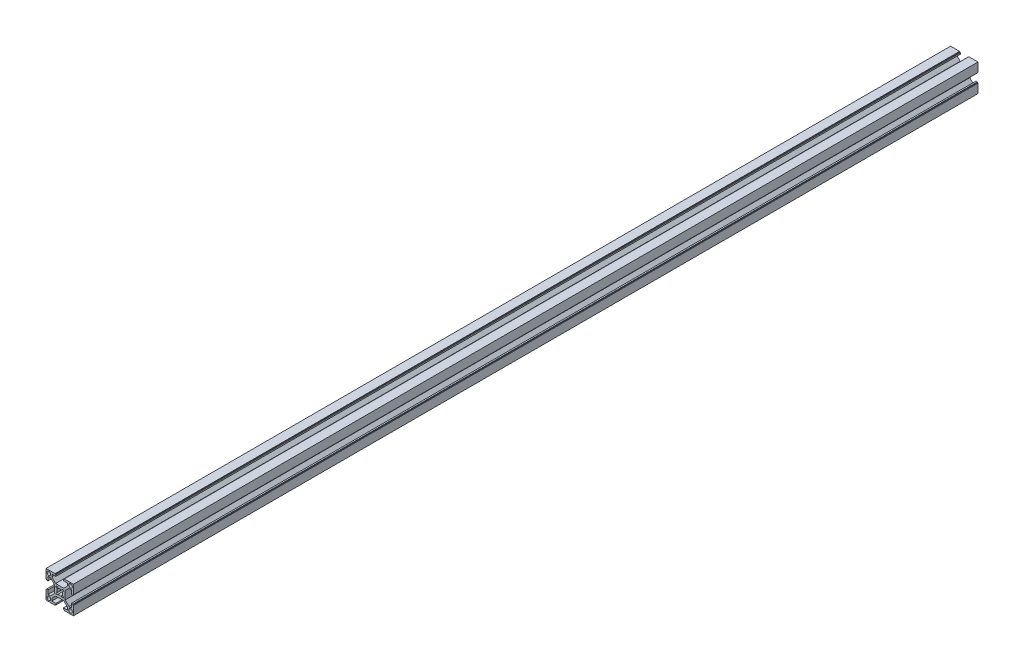
SolidWorks part; units mm, degrees
ref_plane "Front Plane" through (0, 0, 0) normal (0, 0, 1) x (1, 0, 0)
ref_plane "Top Plane" through (0, 0, 0) normal (0, 1, 0) x (1, 0, 0)
ref_plane "Right Plane" through (0, 0, 0) normal (1, 0, 0) x (0, 0, -1)
sketch "Sketch2" plane through (0, 0, 0) normal (0, 0, 1) x (1, 0, 0)
  line L0 (0, 0) -> (0, 10)
  line L1 (0, 0) -> (10, 0)
  line L2 (0, 10) -> (0.7, 10)
  line L3 (0.7, 10) -> (0.7, 10.9)
  line L4 (0.7, 10.9) -> (2.2, 10.9)
  line L5 (2.2, 10.9) -> (2.2, 6.4)
  line L6 (10, 0) -> (10, 0.7)
  line L7 (10, 0.7) -> (10.9, 0.7)
  line L8 (10.9, 0.7) -> (10.9, 2.2)
  line L9 (10.9, 2.2) -> (6.4, 2.2)
  line L10 (2.2, 6.4) -> (4.9, 6.4)
  line L11 (6.4, 2.2) -> (6.4, 4.9)
  line L12 (6.4, 4.9) -> (10.6426, 9.1426)
  line L13 (4.9, 6.4) -> (9.1426, 10.6426)
  line L14 (6.4, 4.9) -> (18.1964, 4.9) construction
  line L15 (4.9, 6.4) -> (7.45, 6.4) construction
  line L16 (10.6426, 9.1426) -> (19.6426, 9.1426)
  line L17 (9.1426, 10.6426) -> (9.1426, 19.6426)
  line L18 (25.3853, 6.4) -> (22.8353, 6.4) construction
  line L19 (23.8853, 4.9) -> (12.0888, 4.9) construction
  line L20 (15.1426, 5.8755) -> (15.1426, 30.9243) construction
  line L21 (21.1426, 10.6426) -> (21.1426, 19.6426)
  line L22 (25.3853, 6.4) -> (21.1426, 10.6426)
  line L23 (23.8853, 4.9) -> (19.6426, 9.1426)
  line L24 (23.8853, 2.2) -> (23.8853, 4.9)
  line L25 (28.0853, 6.4) -> (25.3853, 6.4)
  line L26 (19.3853, 2.2) -> (23.8853, 2.2)
  line L27 (19.3853, 0.7) -> (19.3853, 2.2)
  line L28 (20.2853, 0.7) -> (19.3853, 0.7)
  line L29 (20.2853, 0) -> (20.2853, 0.7)
  line L30 (28.0853, 10.9) -> (28.0853, 6.4)
  line L31 (29.5853, 10.9) -> (28.0853, 10.9)
  line L32 (29.5853, 10) -> (29.5853, 10.9)
  line L33 (30.2853, 10) -> (29.5853, 10)
  line L34 (30.2853, 0) -> (20.2853, 0)
  line L35 (30.2853, 0) -> (30.2853, 10)
  line L36 (-3.9056, 15.1426) -> (38.0923, 15.1426) construction
  line L37 (15.1426, 24.4098) -> (15.1426, -0.6391) construction
  line L38 (23.8853, 25.3853) -> (12.0888, 25.3853) construction
  line L39 (25.3853, 23.8853) -> (22.8353, 23.8853) construction
  line L40 (4.9, 23.8853) -> (7.45, 23.8853) construction
  line L41 (6.4, 25.3853) -> (18.1964, 25.3853) construction
  line L42 (30.2853, 30.2853) -> (30.2853, 20.2853)
  line L43 (30.2853, 30.2853) -> (20.2853, 30.2853)
  line L44 (30.2853, 20.2853) -> (29.5853, 20.2853)
  line L45 (29.5853, 20.2853) -> (29.5853, 19.3853)
  line L46 (29.5853, 19.3853) -> (28.0853, 19.3853)
  line L47 (28.0853, 19.3853) -> (28.0853, 23.8853)
  line L48 (20.2853, 30.2853) -> (20.2853, 29.5853)
  line L49 (20.2853, 29.5853) -> (19.3853, 29.5853)
  line L50 (19.3853, 29.5853) -> (19.3853, 28.0853)
  line L51 (19.3853, 28.0853) -> (23.8853, 28.0853)
  line L52 (28.0853, 23.8853) -> (25.3853, 23.8853)
  line L53 (23.8853, 28.0853) -> (23.8853, 25.3853)
  line L54 (23.8853, 25.3853) -> (19.6426, 21.1426)
  line L55 (25.3853, 23.8853) -> (21.1426, 19.6426)
  line L56 (10.6426, 21.1426) -> (19.6426, 21.1426)
  line L57 (4.9, 23.8853) -> (9.1426, 19.6426)
  line L58 (6.4, 25.3853) -> (10.6426, 21.1426)
  line L59 (6.4, 28.0853) -> (6.4, 25.3853)
  line L60 (2.2, 23.8853) -> (4.9, 23.8853)
  line L61 (10.9, 28.0853) -> (6.4, 28.0853)
  line L62 (10.9, 29.5853) -> (10.9, 28.0853)
  line L63 (10, 29.5853) -> (10.9, 29.5853)
  line L64 (10, 30.2853) -> (10, 29.5853)
  line L65 (2.2, 19.3853) -> (2.2, 23.8853)
  line L66 (0.7, 19.3853) -> (2.2, 19.3853)
  line L67 (0.7, 20.2853) -> (0.7, 19.3853)
  line L68 (0, 20.2853) -> (0.7, 20.2853)
  line L69 (0, 30.2853) -> (10, 30.2853)
  line L70 (0, 30.2853) -> (0, 20.2853)
  point P29 (15.1426, 9.1426)
  point P65 (21.1426, 15.1426)
  point P66 (9.1426, 15.1426)
  point P78 (15.1426, 21.1426)
  dimension "D1" = 10
  dimension "D2" = 10
  dimension "D3" = 0.7
  dimension "D4" = 0.9
  dimension "D5" = 1.5
  dimension "D6" = 4.5
  dimension "D7" = 0.7
  dimension "D8" = 1.5
  dimension "D9" = 0.9
  dimension "D10" = 2.7
  dimension "D11" = 4.5
  dimension "D12" = 6
  dimension "D13" = 45
  dimension "D14" = 45
  dimension "D15" = 2.7
  dimension "D16" = 6
  dimension "D17" = 6
  dimension "D18" = 4.5
  dimension "D19" = 4.5
  dimension "D20" = 2.1213
extrude "Boss-Extrude2" add sketch "Sketch2" against normal blind 1000
sketch "Sketch3" plane through (0, 0, 0) normal (0, 0, 1) x (1, 0, 0)
  line L10 (15.1426, 15.1428) -> (15.1426, 11.8926) construction
  line L20 (3.2001, 27.0853) -> (18.9964, 11.2889) construction
  line L21 (11.2889, 17.865) -> (12.3496, 16.8044)
  line L22 (12.4203, 18.9964) -> (13.481, 17.9357)
  line L24 (17.865, 18.9964) -> (16.8043, 17.9357)
  line L25 (18.9964, 17.865) -> (17.9357, 16.8044)
  line L26 (18.9964, 12.4203) -> (17.9357, 13.4809)
  line L27 (17.865, 11.2889) -> (16.8043, 12.3496)
  line L28 (12.4203, 11.2889) -> (13.481, 12.3496)
  line L29 (11.2889, 12.4203) -> (12.3496, 13.4809)
  line L30 (15.1426, 15.1428) -> (15.1425, 15.1426) construction
  line L32 (15.1425, 15.1426) -> (15.1426, 15.1426) construction
  line L33 (15.1426, 15.1426) -> (15.1425, 15.1426) construction
  circle A0 centre (3.2001, 27.0853) radius 2
  circle A1 centre (27.0852, 27.0853) radius 2
  circle A2 centre (27.0852, 3.1999) radius 2
  circle A3 centre (3.1999, 3.2001) radius 2
  arc A4 (12.3496, 16.8044) -> (12.3496, 13.4809) centre (15.1426, 15.1426) ccw
  arc A5 (11.2889, 17.865) -> (12.4203, 18.9964) centre (11.8546, 18.4307) cw
  arc A6 (18.9964, 17.865) -> (17.865, 18.9964) centre (18.4307, 18.4307) ccw
  arc A7 (18.9964, 12.4203) -> (17.865, 11.2889) centre (18.4307, 11.8546) cw
  arc A8 (11.2889, 12.4203) -> (12.4203, 11.2889) centre (11.8546, 11.8546) ccw
  arc A9 (16.8043, 17.9357) -> (13.481, 17.9357) centre (15.1426, 15.1426) ccw
  arc A10 (17.9357, 13.4809) -> (17.9357, 16.8044) centre (15.1426, 15.1426) ccw
  arc A11 (13.481, 12.3496) -> (16.8043, 12.3496) centre (15.1426, 15.1426) ccw
  point P10 (4.2875, 25.7364)
  dimension "D1" = 4
  dimension "D2" = 6.5
  dimension "D7" = 0.8
  dimension "D3" = 0.8
  dimension "D4" = 0.8
  dimension "D5" = 1.5
  dimension "D6" = 1.5
extrude "Cut-Extrude1" cut sketch "Sketch3" against normal up to next
